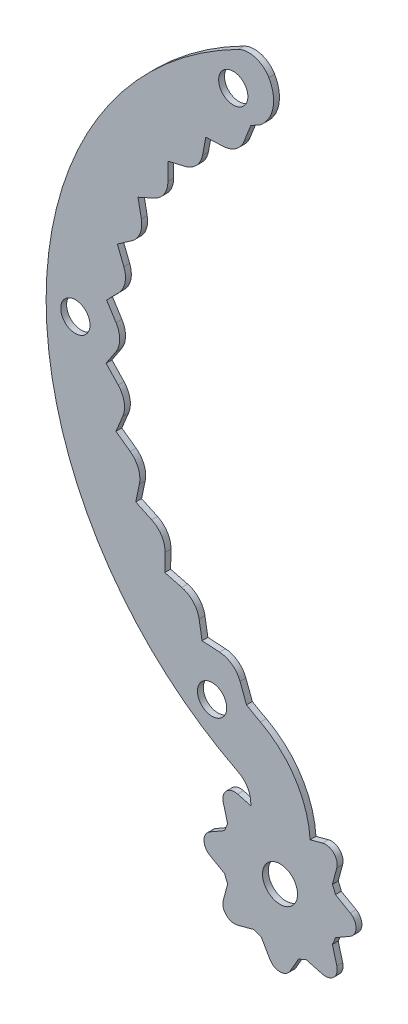
SolidWorks part; units mm, degrees
material "3003 Alaşım"
ref_plane "Ön Düzlem" through (0, 0, 0) normal (0, 0, 1) x (1, 0, 0)
ref_plane "Üst Düzlem" through (0, 0, 0) normal (0, 1, 0) x (1, 0, 0)
ref_plane "Sağ Düzlem" through (0, 0, 0) normal (1, 0, 0) x (0, 0, -1)
sketch "Çizim1" plane through (0, 0, 0) normal (0, 0, 1) x (1, 0, 0)
  line L0 (-50, 0) -> (-25, 0) construction
  line L1 (-25, 74.7114) -> (-25, -57.8833) construction
  line L3 (-25, 43.3013) -> (-26.1465, 40.3921)
  line L10 (-32.6937, 37.73) -> (-33.2521, 34.7773)
  line L11 (-32.6937, 37.73) -> (-29.6915, 37.8626)
  line L12 (-39.1845, 30.9355) -> (-36.2603, 31.6283)
  line L13 (-39.1845, 30.9355) -> (-39.1797, 27.9304)
  line L14 (-44.2872, 23.0451) -> (-41.5446, 24.2736)
  line L15 (-44.2872, 23.0451) -> (-43.7194, 20.0942)
  line L16 (-47.8209, 14.3384) -> (-45.3571, 16.059)
  line L17 (-47.8209, 14.3384) -> (-46.7103, 11.546)
  line L18 (-49.6606, 5.1236) -> (-47.5629, 7.2754)
  line L19 (-49.6606, 5.1236) -> (-48.0464, 2.5889)
  line L20 (-49.7411, -4.2726) -> (-48.0837, -1.7658)
  line L21 (-49.7411, -4.2726) -> (-47.6805, -6.46)
  line L22 (-48.0594, -13.5175) -> (-46.9011, -10.7445)
  line L23 (-48.0594, -13.5175) -> (-45.6255, -15.28)
  line L24 (-44.6753, -22.2835) -> (-44.057, -19.3426)
  line L25 (-44.6753, -22.2835) -> (-41.9541, -23.5587)
  line L26 (-39.7084, -30.2601) -> (-39.6522, -27.2555)
  line L27 (-39.7084, -30.2601) -> (-36.7965, -31.0028)
  line L28 (-33.3349, -37.1647) -> (-33.8427, -34.2028)
  line L29 (-33.3349, -37.1647) -> (-30.3354, -37.3487)
  line L30 (-25.7378, -42.8669) -> (-26.8343, -39.9385)
  line L31 (-25, -57.0526) -> (-25, -57.8833)
  line L33 (-15, -47.697) -> (-15, -66.5436) construction
  line L34 (-25, -66.5436) -> (-15, -66.5436) construction
  line L35 (-25, -54.5436) -> (-25, -66.5436) construction
  arc A0 (-27.1796, 53.4909) -> (-27.1875, -53.4868) centre (0, 0) ccw
  arc A3 (-23.4461, 44.162) -> (-21.9062, 51.9296) centre (-27.0983, 48.9224) ccw
  arc A4 (-26.1465, 40.3921) -> (-29.6915, 37.8626) centre (-29.8679, 41.8587) cw
  arc A5 (-33.2521, 34.7773) -> (-36.2603, 31.6283) centre (-37.1824, 35.5206) cw
  arc A6 (-39.1797, 27.9304) -> (-41.5446, 24.2736) centre (-43.1797, 27.9241) cw
  arc A7 (-43.7194, 20.0942) -> (-45.3571, 16.059) centre (-47.6474, 19.3384) cw
  arc A8 (-46.7103, 11.546) -> (-47.5629, 7.2754) centre (-50.4271, 10.0677) cw
  arc A9 (-48.0464, 2.5889) -> (-48.0837, -1.7658) centre (-51.4203, 0.4403) cw
  arc A10 (-47.6805, -6.46) -> (-46.9011, -10.7445) centre (-50.592, -9.2028) cw
  arc A11 (-45.6255, -15.28) -> (-44.057, -19.3426) centre (-47.9715, -18.5198) cw
  arc A12 (-41.9541, -23.5587) -> (-39.6522, -27.2555) centre (-43.6515, -27.1807) cw
  arc A13 (-36.7965, -31.0028) -> (-33.8427, -34.2028) centre (-37.7852, -34.8787) cw
  arc A14 (-30.3354, -37.3487) -> (-26.8343, -39.9385) centre (-30.5803, -41.3412) cw
  arc A15 (-23.4461, 44.162) -> (-25, 43.3013) centre (0, 0) ccw
  arc A16 (-20.8333, 45.453) -> (-15, -47.697) centre (0, 0) ccw construction
  arc A17 (-23.3522, -44.2117) -> (-14.8293, -57.9841) centre (-30.8249, -58.3594) cw
  arc A18 (-25, -57.8833) -> (-14.8293, -57.9841) centre (-20, -66.5436) ccw
  arc A19 (-25, 54.5436) -> (-25, -54.5436) centre (0, 0) ccw construction
  arc A20 (-27.1875, -53.4868) -> (-25, -57.0526) centre (-29, -57.0526) cw
  arc A21 (-27.1796, 53.4909) -> (-21.9062, 51.9296) centre (-25.3676, 49.9248) cw
  circle A22 centre (-20, -66.5436) radius 5
  arc A23 (-25.7378, -42.8669) -> (-23.3522, -44.2117) centre (0, 0) ccw
  circle A26 centre (-31.6201, -45.0019) radius 2.5
  circle A27 centre (-55, 0) radius 2.5
  circle A28 centre (-28.0006, 47.3388) radius 2.5
  point P9 (-25, 0)
  point P64 (-25, -54.5436)
  point P69 (0, 0)
  dimension "D1" = 60
  dimension "D2" = 10
  dimension "D4" = 4
  dimension "D6" = 16
  dimension "D7" = 4
  dimension "D8" = 4
  dimension "D9" = 10
  dimension "D3" = 25
  dimension "D5" = 11
extrude "Yükseklik-Ekstrüzyon2" add sketch "Çizim1" along normal blind 1
sketch "Çizim2" plane through (0, 0, 1) normal (0, 0, 1) x (1, 0, 0)
  line L0 (-10, -66.5436) -> (-5, -66.5436) construction
  line L1 (-8, -68.2756) -> (-10.6015, -69.7776)
  line L2 (-8, -64.8115) -> (-10.6015, -63.3095)
  line L3 (-10.29, -73.8041) -> (-11.0675, -70.9025)
  line L4 (-12.7395, -76.2536) -> (-15.6411, -75.4761)
  line L5 (-18.2679, -78.5436) -> (-16.7659, -75.942)
  line L6 (-21.7321, -78.5436) -> (-23.2341, -75.942)
  line L7 (-27.2605, -76.2536) -> (-24.3589, -75.4761)
  line L8 (-29.71, -73.8041) -> (-28.9325, -70.9025)
  line L9 (-32, -68.2756) -> (-29.3985, -69.7776)
  line L10 (-32, -64.8115) -> (-29.3985, -63.3095)
  line L11 (-29.71, -59.283) -> (-28.9325, -62.1847)
  line L12 (-27.2605, -56.8335) -> (-24.3589, -57.611)
  line L13 (-21.7321, -54.5436) -> (-23.2341, -57.1451)
  line L14 (-18.2679, -54.5436) -> (-16.7659, -57.1451)
  line L15 (-12.7395, -56.8335) -> (-15.6411, -57.611)
  line L16 (-10.29, -59.283) -> (-11.0675, -62.1847)
  circle A0 centre (-20, -66.5436) radius 10 construction
  arc A1 (-8, -68.2756) -> (-8, -64.8115) centre (-9, -66.5436) ccw
  arc A2 (-12.7395, -76.2536) -> (-10.29, -73.8041) centre (-12.2218, -74.3217) ccw
  arc A4 (-21.7321, -78.5436) -> (-18.2679, -78.5436) centre (-20, -77.5436) ccw
  arc A6 (-29.71, -73.8041) -> (-27.2605, -76.2536) centre (-27.7782, -74.3217) ccw
  arc A8 (-32, -64.8115) -> (-32, -68.2756) centre (-31, -66.5436) ccw
  circle A9 centre (-20, -66.5436) radius 10 construction
  arc A10 (-27.2605, -56.8335) -> (-29.71, -59.283) centre (-27.7782, -58.7654) ccw
  arc A12 (-18.2679, -54.5436) -> (-21.7321, -54.5436) centre (-20, -55.5436) ccw
  circle A13 centre (-20, -66.5436) radius 10 construction
  arc A14 (-10.29, -59.283) -> (-12.7395, -56.8335) centre (-12.2218, -58.7654) ccw
  arc A17 (-16.7659, -57.1451) -> (-15.6411, -57.611) centre (-15.8999, -56.6451) ccw
  arc A18 (-28.9325, -62.1847) -> (-29.3985, -63.3095) centre (-29.8985, -62.4435) cw
  arc A20 (-29.3985, -69.7776) -> (-28.9325, -70.9025) centre (-29.8985, -70.6436) cw
  arc A22 (-24.3589, -75.4761) -> (-23.2341, -75.942) centre (-24.1001, -76.442) cw
  arc A24 (-16.7659, -75.942) -> (-15.6411, -75.4761) centre (-15.8999, -76.442) cw
  arc A26 (-11.0675, -70.9025) -> (-10.6015, -69.7776) centre (-10.1015, -70.6436) cw
  arc A28 (-10.6015, -63.3095) -> (-11.0675, -62.1847) centre (-10.1015, -62.4435) cw
  arc A30 (-24.3589, -57.611) -> (-23.2341, -57.1451) centre (-24.1001, -56.6451) ccw
  circle A32 centre (-20, -66.5436) radius 10 [skipped]
  circle A33 centre (-20, -66.5436) radius 10 [skipped]
  circle A34 centre (-20, -66.5436) radius 10 [skipped]
  circle A35 centre (-20, -66.5436) radius 10 [skipped]
  circle A36 centre (-20, -66.5436) radius 10 [skipped]
  circle A37 centre (-20, -66.5436) radius 3
  point P54 (-20, -66.5436)
  dimension "D2" = 2
  dimension "D5" = 1
  dimension "D4" = 1
  dimension "D1" = 30
  dimension "D3" = 8
extrude "Yükseklik-Ekstrüzyon4" add sketch "Çizim2" against normal blind 1
